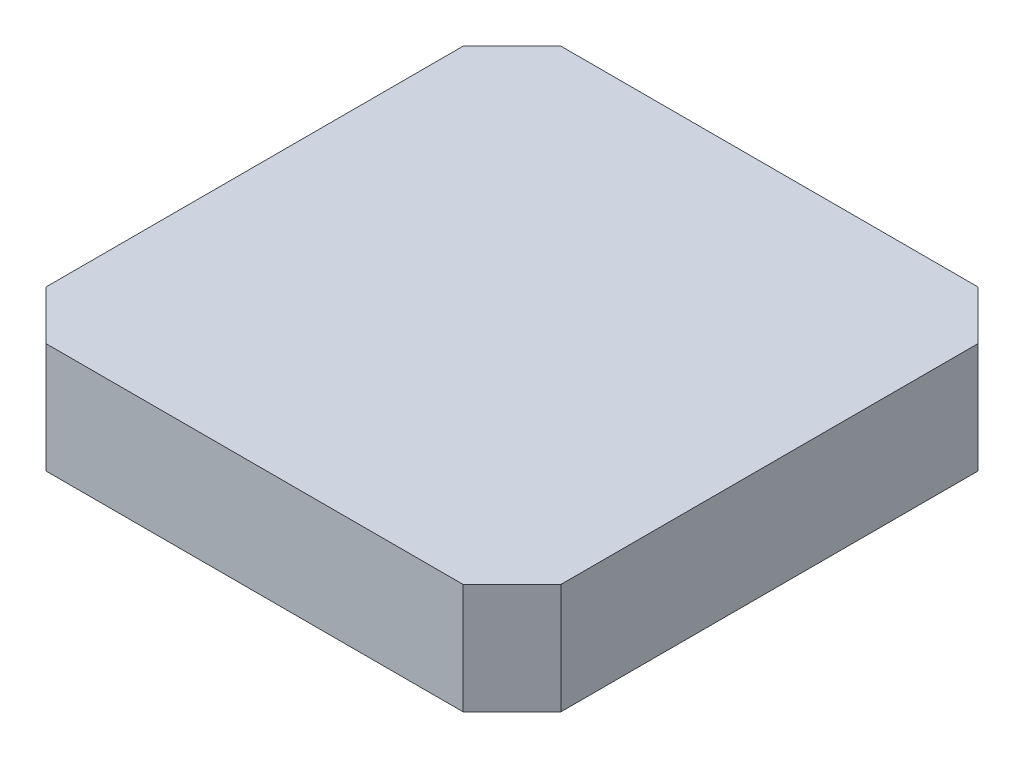
SolidWorks part; units mm, degrees
ref_plane "Front Plane" through (0, 0, 0) normal (0, 0, 1) x (1, 0, 0)
ref_plane "Top Plane" through (0, 0, 0) normal (0, 1, 0) x (1, 0, 0)
ref_plane "Right Plane" through (0, 0, 0) normal (1, 0, 0) x (0, 0, -1)
sketch "Sketch1" plane through (0, 0, 0) normal (0, 1, 0) x (1, 0, 0)
  line L1 (-21, 21) -> (21, 21)
  line L2 (-21, 21) -> (-21, -21)
  line L3 (-21, -21) -> (21, -21)
  line L4 (21, 21) -> (21, -21)
  point P4 (0, 21)
  point P6 (21, 0)
  dimension "D1" = 42
  dimension "D2" = 42
extrude "Boss-Extrude1" add sketch "Sketch1" along normal blind 9
chamfer "Chamfer1" distance 4 angle 45 4 edges at (21, 4.5, -21) (21, 4.5, 21) (-21, 4.5, -21) (-21, 4.5, 21)
sketch "Sketch2" plane through (0, 0, 0) normal (0, -1, 0) x (1, 0, 0)
  circle A0 centre (0, 0) radius 4
extrude "Cut-Extrude2" cut sketch "Sketch2" against normal blind 3 draft 3 draft outward yes
